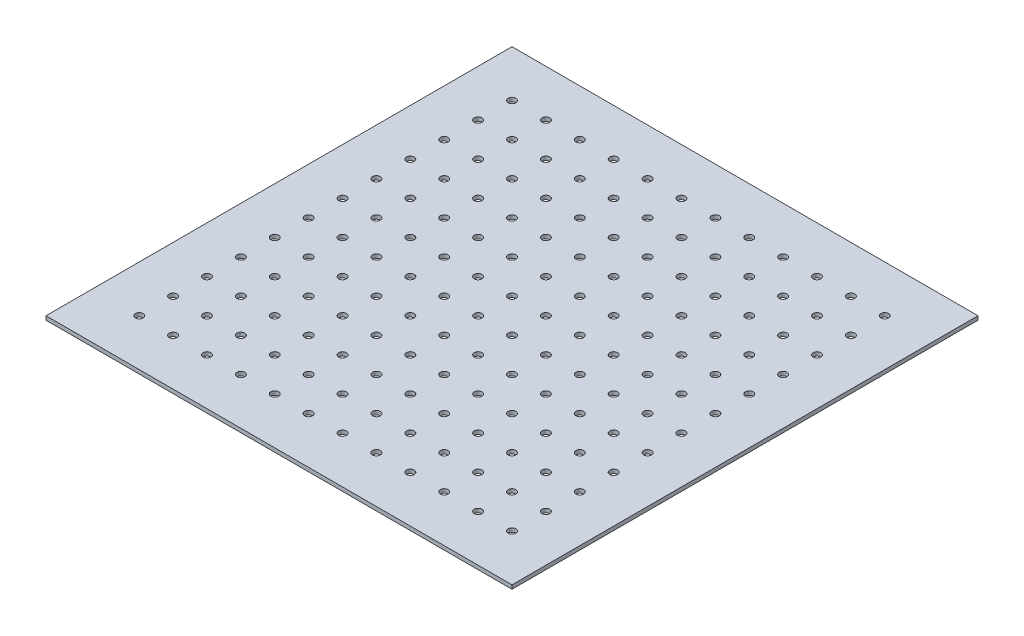
SolidWorks part; units mm, degrees
ref_plane "Front Plane" through (0, 0, 0) normal (0, 0, 1) x (1, 0, 0)
ref_plane "Top Plane" through (0, 0, 0) normal (0, 1, 0) x (1, 0, 0)
ref_plane "Right Plane" through (0, 0, 0) normal (1, 0, 0) x (0, 0, -1)
sketch "Sketch1" plane through (0, 0, 0) normal (0, 1, 0) x (1, 0, 0)
  line L1 (-190.5, -190.5) -> (190.5, -190.5)
  line L2 (-190.5, -190.5) -> (-190.5, 190.5)
  line L3 (-190.5, 190.5) -> (190.5, 190.5)
  line L4 (190.5, -190.5) -> (190.5, 190.5)
  line L5 (-190.5, -190.5) -> (190.5, 190.5) construction
  line L6 (-190.5, 190.5) -> (190.5, -190.5) construction
  circle A0 centre (-152.4, 152.4) radius 3.175
  circle A1 centre (-124.6909, 152.4) radius 3.175
  circle A2 centre (-96.9818, 152.4) radius 3.175
  circle A3 centre (-69.2727, 152.4) radius 3.175
  circle A4 centre (-41.5636, 152.4) radius 3.175
  circle A5 centre (-13.8545, 152.4) radius 3.175
  circle A6 centre (13.8545, 152.4) radius 3.175
  circle A7 centre (41.5636, 152.4) radius 3.175
  circle A8 centre (69.2727, 152.4) radius 3.175
  circle A9 centre (96.9818, 152.4) radius 3.175
  circle A10 centre (124.6909, 152.4) radius 3.175
  circle A11 centre (152.4, 152.4) radius 3.175
  circle A12 centre (-124.6909, 124.6909) radius 3.175
  circle A13 centre (-96.9818, 124.6909) radius 3.175
  circle A14 centre (-69.2727, 124.6909) radius 3.175
  circle A15 centre (-41.5636, 124.6909) radius 3.175
  circle A16 centre (-13.8545, 124.6909) radius 3.175
  circle A17 centre (13.8545, 124.6909) radius 3.175
  circle A18 centre (41.5636, 124.6909) radius 3.175
  circle A19 centre (69.2727, 124.6909) radius 3.175
  circle A20 centre (96.9818, 124.6909) radius 3.175
  circle A21 centre (124.6909, 124.6909) radius 3.175
  circle A22 centre (152.4, 124.6909) radius 3.175
  circle A23 centre (-124.6909, 96.9818) radius 3.175
  circle A24 centre (-96.9818, 96.9818) radius 3.175
  circle A25 centre (-69.2727, 96.9818) radius 3.175
  circle A26 centre (-41.5636, 96.9818) radius 3.175
  circle A27 centre (-13.8545, 96.9818) radius 3.175
  circle A28 centre (13.8545, 96.9818) radius 3.175
  circle A29 centre (41.5636, 96.9818) radius 3.175
  circle A30 centre (69.2727, 96.9818) radius 3.175
  circle A31 centre (96.9818, 96.9818) radius 3.175
  circle A32 centre (124.6909, 96.9818) radius 3.175
  circle A33 centre (152.4, 96.9818) radius 3.175
  circle A34 centre (-124.6909, 69.2727) radius 3.175
  circle A35 centre (-96.9818, 69.2727) radius 3.175
  circle A36 centre (-69.2727, 69.2727) radius 3.175
  circle A37 centre (-41.5636, 69.2727) radius 3.175
  circle A38 centre (-13.8545, 69.2727) radius 3.175
  circle A39 centre (13.8545, 69.2727) radius 3.175
  circle A40 centre (41.5636, 69.2727) radius 3.175
  circle A41 centre (69.2727, 69.2727) radius 3.175
  circle A42 centre (96.9818, 69.2727) radius 3.175
  circle A43 centre (124.6909, 69.2727) radius 3.175
  circle A44 centre (152.4, 69.2727) radius 3.175
  circle A45 centre (-124.6909, 41.5636) radius 3.175
  circle A46 centre (-96.9818, 41.5636) radius 3.175
  circle A47 centre (-69.2727, 41.5636) radius 3.175
  circle A48 centre (-41.5636, 41.5636) radius 3.175
  circle A49 centre (-13.8545, 41.5636) radius 3.175
  circle A50 centre (13.8545, 41.5636) radius 3.175
  circle A51 centre (41.5636, 41.5636) radius 3.175
  circle A52 centre (69.2727, 41.5636) radius 3.175
  circle A53 centre (96.9818, 41.5636) radius 3.175
  circle A54 centre (124.6909, 41.5636) radius 3.175
  circle A55 centre (152.4, 41.5636) radius 3.175
  circle A56 centre (-124.6909, 13.8545) radius 3.175
  circle A57 centre (-96.9818, 13.8545) radius 3.175
  circle A58 centre (-69.2727, 13.8545) radius 3.175
  circle A59 centre (-41.5636, 13.8545) radius 3.175
  circle A60 centre (-13.8545, 13.8545) radius 3.175
  circle A61 centre (13.8545, 13.8545) radius 3.175
  circle A62 centre (41.5636, 13.8545) radius 3.175
  circle A63 centre (69.2727, 13.8545) radius 3.175
  circle A64 centre (96.9818, 13.8545) radius 3.175
  circle A65 centre (124.6909, 13.8545) radius 3.175
  circle A66 centre (152.4, 13.8545) radius 3.175
  circle A67 centre (-124.6909, -13.8545) radius 3.175
  circle A68 centre (-96.9818, -13.8545) radius 3.175
  circle A69 centre (-69.2727, -13.8545) radius 3.175
  circle A70 centre (-41.5636, -13.8545) radius 3.175
  circle A71 centre (-13.8545, -13.8545) radius 3.175
  circle A72 centre (13.8545, -13.8545) radius 3.175
  circle A73 centre (41.5636, -13.8545) radius 3.175
  circle A74 centre (69.2727, -13.8545) radius 3.175
  circle A75 centre (96.9818, -13.8545) radius 3.175
  circle A76 centre (124.6909, -13.8545) radius 3.175
  circle A77 centre (152.4, -13.8545) radius 3.175
  circle A78 centre (-124.6909, -41.5636) radius 3.175
  circle A79 centre (-96.9818, -41.5636) radius 3.175
  circle A80 centre (-69.2727, -41.5636) radius 3.175
  circle A81 centre (-41.5636, -41.5636) radius 3.175
  circle A82 centre (-13.8545, -41.5636) radius 3.175
  circle A83 centre (13.8545, -41.5636) radius 3.175
  circle A84 centre (41.5636, -41.5636) radius 3.175
  circle A85 centre (69.2727, -41.5636) radius 3.175
  circle A86 centre (96.9818, -41.5636) radius 3.175
  circle A87 centre (124.6909, -41.5636) radius 3.175
  circle A88 centre (152.4, -41.5636) radius 3.175
  circle A89 centre (-124.6909, -69.2727) radius 3.175
  circle A90 centre (-96.9818, -69.2727) radius 3.175
  circle A91 centre (-69.2727, -69.2727) radius 3.175
  circle A92 centre (-41.5636, -69.2727) radius 3.175
  circle A93 centre (-13.8545, -69.2727) radius 3.175
  circle A94 centre (13.8545, -69.2727) radius 3.175
  circle A95 centre (41.5636, -69.2727) radius 3.175
  circle A96 centre (69.2727, -69.2727) radius 3.175
  circle A97 centre (96.9818, -69.2727) radius 3.175
  circle A98 centre (124.6909, -69.2727) radius 3.175
  circle A99 centre (152.4, -69.2727) radius 3.175
  circle A100 centre (-124.6909, -96.9818) radius 3.175
  circle A101 centre (-96.9818, -96.9818) radius 3.175
  circle A102 centre (-69.2727, -96.9818) radius 3.175
  circle A103 centre (-41.5636, -96.9818) radius 3.175
  circle A104 centre (-13.8545, -96.9818) radius 3.175
  circle A105 centre (13.8545, -96.9818) radius 3.175
  circle A106 centre (41.5636, -96.9818) radius 3.175
  circle A107 centre (69.2727, -96.9818) radius 3.175
  circle A108 centre (96.9818, -96.9818) radius 3.175
  circle A109 centre (124.6909, -96.9818) radius 3.175
  circle A110 centre (152.4, -96.9818) radius 3.175
  circle A111 centre (-124.6909, -124.6909) radius 3.175
  circle A112 centre (-96.9818, -124.6909) radius 3.175
  circle A113 centre (-69.2727, -124.6909) radius 3.175
  circle A114 centre (-41.5636, -124.6909) radius 3.175
  circle A115 centre (-13.8545, -124.6909) radius 3.175
  circle A116 centre (13.8545, -124.6909) radius 3.175
  circle A117 centre (41.5636, -124.6909) radius 3.175
  circle A118 centre (69.2727, -124.6909) radius 3.175
  circle A119 centre (96.9818, -124.6909) radius 3.175
  circle A120 centre (124.6909, -124.6909) radius 3.175
  circle A121 centre (152.4, -124.6909) radius 3.175
  circle A122 centre (-124.6909, -152.4) radius 3.175
  circle A123 centre (-96.9818, -152.4) radius 3.175
  circle A124 centre (-69.2727, -152.4) radius 3.175
  circle A125 centre (-41.5636, -152.4) radius 3.175
  circle A126 centre (-13.8545, -152.4) radius 3.175
  circle A127 centre (13.8545, -152.4) radius 3.175
  circle A128 centre (41.5636, -152.4) radius 3.175
  circle A129 centre (69.2727, -152.4) radius 3.175
  circle A130 centre (96.9818, -152.4) radius 3.175
  circle A131 centre (124.6909, -152.4) radius 3.175
  circle A132 centre (152.4, -152.4) radius 3.175
  circle A133 centre (-152.4, 124.6909) radius 3.175
  circle A134 centre (-152.4, 96.9818) radius 3.175
  circle A135 centre (-152.4, 69.2727) radius 3.175
  circle A136 centre (-152.4, 41.5636) radius 3.175
  circle A137 centre (-152.4, 13.8545) radius 3.175
  circle A138 centre (-152.4, -13.8545) radius 3.175
  circle A139 centre (-152.4, -41.5636) radius 3.175
  circle A140 centre (-152.4, -69.2727) radius 3.175
  circle A141 centre (-152.4, -96.9818) radius 3.175
  circle A142 centre (-152.4, -124.6909) radius 3.175
  circle A143 centre (-152.4, -152.4) radius 3.175
  point P0 (0, 0)
  point P8 (152.4, -152.4)
  point P9 (0, 0)
  point P10 (0, 0)
  dimension "D2" = 6.35
  dimension "D1" = 381
  dimension "D5" = 38.1
  dimension "D6" = 38.1
  dimension "D3" = 12
  dimension "D4" = 12
extrude "Boss-Extrude1" add sketch "Sketch1" along normal blind 3.175
